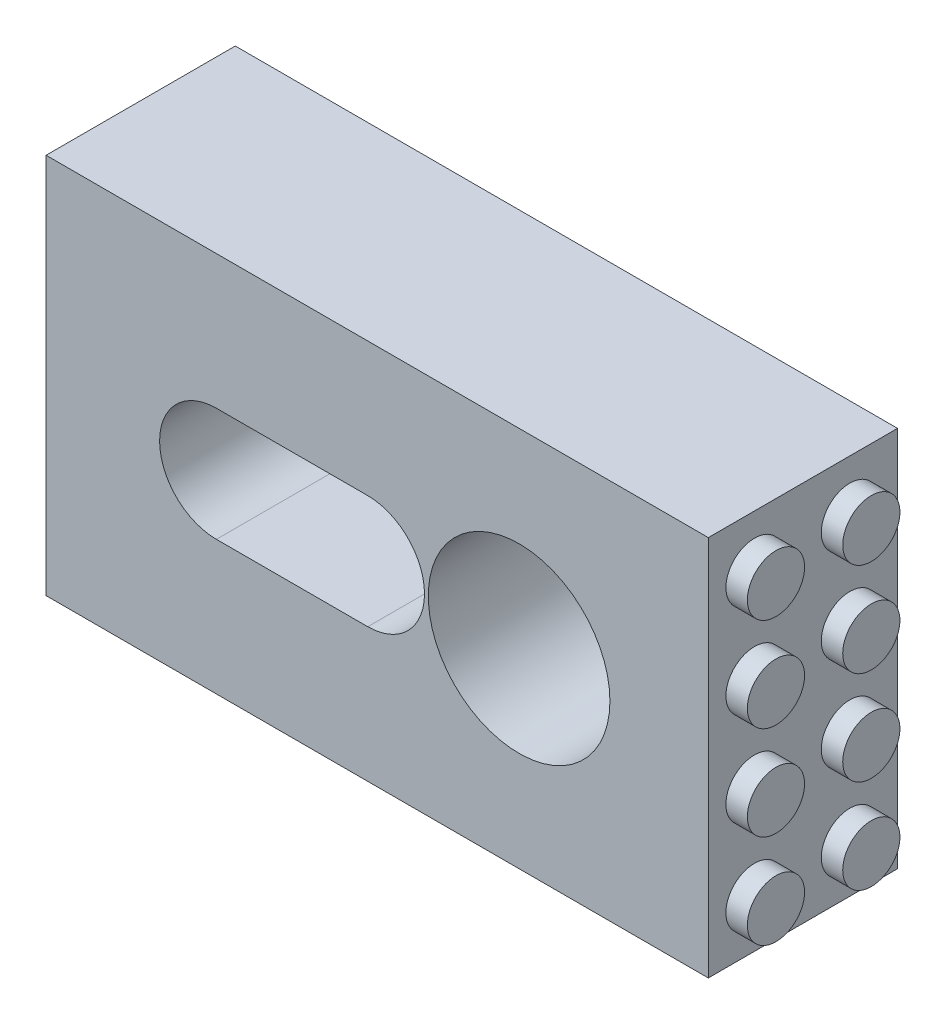
SolidWorks part; units mm, degrees
material "Custom Plastic"
ref_plane "Front Plane" through (0, 0, 0) normal (0, 0, 1) x (1, 0, 0)
ref_plane "Top Plane" through (0, 0, 0) normal (0, 1, 0) x (1, 0, 0)
ref_plane "Right Plane" through (0, 0, 0) normal (1, 0, 0) x (0, 0, -1)
sketch "Sketch1" plane through (0, 0, 0) normal (0, 1, 0) x (1, 0, 0)
  line L1 (-94.449, 51.0406) -> (-38.8865, 51.0406)
  line L2 (-94.449, 51.0406) -> (-94.449, 19.2906)
  line L3 (-94.449, 19.2906) -> (-38.8865, 19.2906)
  line L4 (-38.8865, 51.0406) -> (-38.8865, 19.2906)
  dimension "D1" = 55.5625
  dimension "D2" = 31.75
extrude "Boss-Extrude1" add sketch "Sketch1" along normal blind 28.575
sketch "Sketch2" plane through (0, 0, -19.2906) normal (0, 0, 1) x (1, 0, 0)
  line L1 (-94.449, 0) -> (-38.8865, 0) construction
  line L2 (-38.8865, 28.575) -> (-38.8865, 0) construction
  circle A0 centre (-54.7615, 16) radius 7.62
  dimension "D3" = 15.24
  dimension "D1" = 16
  dimension "D2" = 15.875
extrude "Cut-Extrude1" cut sketch "Sketch2" against normal blind 13.335
sketch "Sketch3" plane through (0, 0, -19.2906) normal (0, 0, 1) x (1, 0, 0)
  line L0 (-94.449, 28.575) -> (-38.8865, 28.575) construction
  line L1 (-94.449, 28.575) -> (-38.8865, 28.575)
  line L2 (-80.1615, 16) -> (-67.4615, 16) construction
  line L3 (-80.1615, 20.7625) -> (-67.4615, 20.7625)
  line L4 (-80.1615, 11.2375) -> (-67.4615, 11.2375)
  line L6 (-94.449, 0) -> (-38.8865, 0) construction
  arc A0 (-80.1615, 20.7625) -> (-80.1615, 11.2375) centre (-80.1615, 16) ccw
  circle A1 centre (-54.7615, 16) radius 7.62
  circle A2 centre (-54.7615, 16) radius 7.62
  arc A3 (-67.4615, 11.2375) -> (-67.4615, 20.7625) centre (-67.4615, 16) ccw
  point P7 (-73.8115, 16)
  dimension "D4" = 4.7625
  dimension "D5" = 16
  dimension "D2" = 12.7
  dimension "D3" = 12.7
  dimension "D1" = 0
extrude "Cut-Extrude2" cut sketch "Sketch3" against normal blind 12.7
sketch "Sketch4" plane through (0, 0, -31.9906) normal (0, 0, 1) x (1, 0, 0)
  line L2 (-80.1615, 11.2375) -> (-67.4615, 11.2375)
  line L3 (-67.4615, 20.7625) -> (-80.1615, 20.7625)
  line L4 (-80.1615, 11.2375) -> (-67.4615, 11.2375)
  line L5 (-67.4615, 20.7625) -> (-80.1615, 20.7625)
  arc A2 (-67.4615, 11.2375) -> (-67.4615, 20.7625) centre (-67.4615, 16) ccw
  arc A3 (-80.1615, 20.7625) -> (-80.1615, 11.2375) centre (-80.1615, 16) ccw
  arc A4 (-67.4615, 11.2375) -> (-67.4615, 20.7625) centre (-67.4615, 16) ccw
  arc A5 (-80.1615, 20.7625) -> (-80.1615, 11.2375) centre (-80.1615, 16) ccw
  circle A6 centre (-80.1615, 16) radius 1.8415
  circle A7 centre (-67.4615, 16) radius 1.8415
  dimension "D2" = 3.683
  dimension "D3" = 3.683
  dimension "D1" = 0
extrude "Cut-Extrude3" cut sketch "Sketch4" against normal blind 25.4 contours A7 | A6
sketch "Sketch5" plane through (0, 0, -51.0406) normal (0, 0, -1) x (-1, 0, 0)
  line L2 (67.4615, 11.2375) -> (80.1615, 11.2375)
  line L3 (80.1615, 20.7625) -> (67.4615, 20.7625)
  line L4 (38.8865, 0) -> (94.449, 0)
  line L5 (94.449, 0) -> (94.449, 28.575)
  line L6 (94.449, 28.575) -> (38.8865, 28.575)
  line L7 (38.8865, 28.575) -> (38.8865, 0)
  line L8 (38.8865, 0) -> (94.449, 0)
  line L9 (94.449, 0) -> (94.449, 28.575)
  line L10 (94.449, 28.575) -> (38.8865, 28.575)
  line L11 (38.8865, 28.575) -> (38.8865, 0)
  line L12 (67.4615, 11.2375) -> (80.1615, 11.2375)
  line L13 (80.1615, 20.7625) -> (67.4615, 20.7625)
  arc A2 (67.4615, 20.7625) -> (67.4615, 11.2375) centre (67.4615, 16) ccw
  arc A3 (80.1615, 11.2375) -> (80.1615, 20.7625) centre (80.1615, 16) ccw
  arc A4 (67.4615, 20.7625) -> (67.4615, 11.2375) centre (67.4615, 16) ccw
  arc A5 (80.1615, 11.2375) -> (80.1615, 20.7625) centre (80.1615, 16) ccw
  dimension "D1" = 0
  dimension "D2" = 0
extrude "Cut-Extrude4" cut sketch "Sketch5" against normal blind 17.78 contours L13 A4 L12 A5
sketch "Sketch6" plane through (0, 0, -51.0406) normal (0, 0, -1) x (-1, 0, 0)
  line L4 (38.8865, 0) -> (94.449, 0)
  line L5 (94.449, 0) -> (94.449, 28.575)
  line L6 (94.449, 28.575) -> (38.8865, 28.575)
  line L7 (38.8865, 28.575) -> (38.8865, 0)
  line L8 (38.8865, 0) -> (94.449, 0)
  line L9 (94.449, 0) -> (94.449, 28.575)
  line L10 (94.449, 28.575) -> (38.8865, 28.575)
  line L11 (38.8865, 28.575) -> (38.8865, 0)
  dimension "D1" = 0
extrude "Cut-Extrude5" cut sketch "Sketch6" against normal blind 15.875
sketch "Sketch7" plane through (0, 0, -32.6256) normal (0, 0, 1) x (1, 0, 0)
  line L0 (-94.449, 0) -> (-38.8865, 0) construction
  circle A0 centre (-54.7615, 16) radius 2.7781
  dimension "D2" = 5.5562
  dimension "D1" = 16
extrude "Cut-Extrude7" cut sketch "Sketch7" against normal blind 7.9375
sketch "Sketch8" plane through (-38.8865, 0, 0) normal (1, 0, 0) x (0, 0, -1)
  line L2 (35.1656, 28.575) -> (35.1656, 0) construction
  line L3 (19.2906, 0) -> (35.1656, 0) construction
  circle A0 centre (31.1656, 4) radius 2.4
  circle A1 centre (23.1656, 4) radius 2.4
  circle A2 centre (23.1656, 11.874) radius 2.4
  circle A3 centre (31.1656, 11.874) radius 2.4
  circle A4 centre (23.1656, 19.748) radius 2.4
  circle A5 centre (31.1656, 19.748) radius 2.4
  circle A6 centre (23.1656, 27.622) radius 2.4
  circle A7 centre (31.1656, 27.622) radius 2.4
  dimension "D1" = 4.8
  dimension "D2" = 4
  dimension "D4" = 4.8
  dimension "D3" = 8
  dimension "D5" = 4
  dimension "D6" = 4
extrude "Boss-Extrude2" add sketch "Sketch8" along normal blind 1.8
sketch "Sketch10" plane through (0, 28.575, 0) normal (0, 1, 0) x (1, 0, 0)
  line L8 (-38.8865, 19.2906) -> (-38.8865, 20.9629)
  line L9 (-38.8865, 20.9629) -> (-38.8865, 25.3683)
  line L10 (-38.8865, 25.3683) -> (-38.8865, 28.9629)
  line L11 (-38.8865, 28.9629) -> (-38.8865, 33.3683)
  line L12 (-38.8865, 33.3683) -> (-38.8865, 35.1656)
  line L13 (-38.8865, 35.1656) -> (-94.449, 35.1656)
  line L14 (-94.449, 35.1656) -> (-94.449, 19.2906)
  line L15 (-94.449, 19.2906) -> (-38.8865, 19.2906)
  line L16 (-38.8865, 19.2906) -> (-38.8865, 20.9629)
  line L17 (-38.8865, 20.9629) -> (-38.8865, 25.3683)
  line L18 (-38.8865, 25.3683) -> (-38.8865, 28.9629)
  line L19 (-38.8865, 28.9629) -> (-38.8865, 33.3683)
  line L20 (-38.8865, 33.3683) -> (-38.8865, 35.1656)
  line L21 (-38.8865, 35.1656) -> (-94.449, 35.1656)
  line L22 (-94.449, 35.1656) -> (-94.449, 19.2906)
  line L23 (-94.449, 19.2906) -> (-38.8865, 19.2906)
  dimension "D1" = 0
extrude "Boss-Extrude3" add sketch "Sketch10" along normal blind 4
sketch "Sketch11" plane through (0, 0, -19.2906) normal (0, 0, 1) x (1, 0, 0)
  line L3 (-94.449, 32) -> (-38.8865, 32)
  line L4 (-94.449, 0) -> (-38.8865, 0)
  line L5 (-38.8865, 0) -> (-38.8865, 32.575)
  line L6 (-38.8865, 32.575) -> (-94.449, 32.575)
  line L7 (-94.449, 32.575) -> (-94.449, 0)
  line L9 (-38.8865, 32) -> (-38.8865, 32.575)
  line L10 (-38.8865, 32.575) -> (-94.449, 32.575)
  dimension "D1" = 0
extrude "Cut-Extrude8" cut sketch "Sketch11" against normal through all and the other way through all
sketch "Sketch12" plane through (-94.449, 0, 0) normal (-1, 0, 0) x (0, 0, 1)
  line L0 (-19.2906, 32) -> (-35.1656, 32) construction
  line L1 (-33.9656, 30.8) -> (-31.4656, 30.8)
  line L2 (-33.9656, 30.8) -> (-33.9656, 28.3)
  line L3 (-33.9656, 1.2) -> (-31.4656, 1.2)
  line L4 (-20.4906, 30.8) -> (-20.4906, 28.3)
  line L5 (-35.1656, 0) -> (-35.1656, 32) construction
  line L6 (-35.1656, 0) -> (-19.2906, 0) construction
  line L7 (-19.2906, 32) -> (-19.2906, 0) construction
  line L8 (-33.9656, 19.826) -> (-33.6656, 19.826)
  line L9 (-33.9656, 28.3) -> (-33.6656, 28.3)
  line L11 (-33.9656, 27.7) -> (-33.6656, 27.7)
  line L12 (-33.6656, 28.3) -> (-33.6656, 27.7)
  line L13 (-20.4906, 28.3) -> (-20.7906, 28.3)
  line L14 (-22.9906, 30.8) -> (-20.4906, 30.8)
  line L15 (-20.4906, 27.7) -> (-20.7906, 27.7)
  line L16 (-20.7906, 28.3) -> (-20.7906, 27.7)
  line L17 (-33.6656, 20.426) -> (-33.6656, 19.826)
  line L18 (-33.9656, 20.426) -> (-33.6656, 20.426)
  line L19 (-20.4906, 19.826) -> (-20.7906, 19.826)
  line L20 (-20.7906, 20.426) -> (-20.7906, 19.826)
  line L21 (-20.4906, 20.426) -> (-20.7906, 20.426)
  line L22 (-33.9656, 11.952) -> (-33.6656, 11.952)
  line L23 (-33.6656, 12.552) -> (-33.6656, 11.952)
  line L24 (-33.9656, 12.552) -> (-33.6656, 12.552)
  line L25 (-20.4906, 11.952) -> (-20.7906, 11.952)
  line L26 (-20.7906, 12.552) -> (-20.7906, 11.952)
  line L27 (-20.4906, 12.552) -> (-20.7906, 12.552)
  line L28 (-33.9656, 4.078) -> (-33.6656, 4.078)
  line L29 (-33.6656, 4.678) -> (-33.6656, 4.078)
  line L30 (-33.9656, 4.678) -> (-33.6656, 4.678)
  line L31 (-20.4906, 4.078) -> (-20.7906, 4.078)
  line L32 (-20.7906, 4.678) -> (-20.7906, 4.078)
  line L33 (-20.4906, 4.678) -> (-20.7906, 4.678)
  line L34 (-33.9656, 19.826) -> (-33.9656, 12.552)
  line L36 (-31.4656, 30.8) -> (-31.4656, 30.5)
  line L37 (-31.4656, 30.5) -> (-30.8656, 30.5)
  line L38 (-30.8656, 30.8) -> (-30.8656, 30.5)
  line L39 (-30.8656, 30.8) -> (-23.5906, 30.8)
  line L40 (-23.5906, 30.8) -> (-23.5906, 30.5)
  line L41 (-23.5906, 30.5) -> (-22.9906, 30.5)
  line L42 (-22.9906, 30.8) -> (-22.9906, 30.5)
  line L43 (-22.9906, 1.2) -> (-22.9906, 1.5)
  line L44 (-23.5906, 1.5) -> (-22.9906, 1.5)
  line L45 (-23.5906, 1.2) -> (-23.5906, 1.5)
  line L46 (-30.8656, 1.2) -> (-30.8656, 1.5)
  line L47 (-31.4656, 1.5) -> (-30.8656, 1.5)
  line L48 (-31.4656, 1.2) -> (-31.4656, 1.5)
  line L49 (-33.9656, 11.952) -> (-33.9656, 4.678)
  line L50 (-20.4906, 19.826) -> (-20.4906, 12.552)
  line L51 (-20.4906, 11.952) -> (-20.4906, 4.678)
  line L52 (-20.4906, 4.078) -> (-20.4906, 1.2)
  line L53 (-33.9656, 4.078) -> (-33.9656, 1.2)
  line L54 (-30.8656, 1.2) -> (-23.5906, 1.2)
  line L55 (-22.9906, 1.2) -> (-20.4906, 1.2)
  line L56 (-20.4906, 27.7) -> (-20.4906, 20.426)
  line L57 (-33.9656, 27.7) -> (-33.9656, 20.426)
  circle A0 centre (-27.2906, 24) radius 3.255
  circle A1 centre (-27.2906, 24) radius 2.45
  circle A2 centre (-27.2906, 16) radius 3.255
  circle A3 centre (-27.2906, 16) radius 2.45
  circle A4 centre (-27.2906, 8) radius 3.255
  circle A5 centre (-27.2906, 8) radius 2.45
  dimension "D6" = 6.51
  dimension "D7" = 4.9
  dimension "D1" = 1.2
  dimension "D2" = 1.2
  dimension "D3" = 1.2
  dimension "D4" = 1.2
  dimension "D5" = 8
  dimension "D9" = 8
  dimension "D10" = 0.6
  dimension "D11" = 0.6
  dimension "D12" = 0.3
  dimension "D13" = 0.3
  dimension "D14" = 4
  dimension "D15" = 0.6
  dimension "D16" = 0.6
  dimension "D17" = 0.3
  dimension "D18" = 0.3
  dimension "D8" = 3
extrude "Cut-Extrude10" cut sketch "Sketch12" against normal blind 2.1 contours A1 | L11 L57 L18 L17 L8 L34 L24 L23 L22 L49 L30 L29 L28 L53 L3 L48 L47 L46 L54 L45 L44 L43 L55 L52 L31 L32 L33 L51 L25 L26 L27 L50 L19 L20 L21 L56 L15 L16 L13 L4 L14 L42 L41 L40 L39 L38 L37 L36 L1 L2 L9 | A5 | A3
